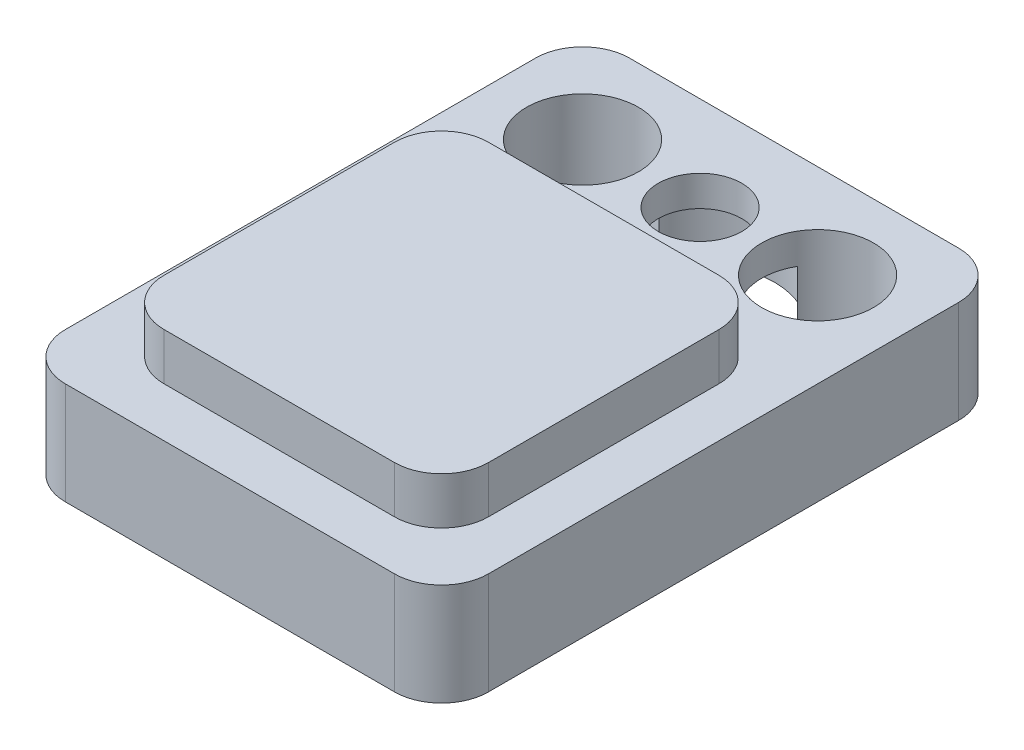
SolidWorks part; units mm, degrees
ref_plane "Front Plane" through (0, 0, 0) normal (0, 0, 1) x (1, 0, 0)
ref_plane "Top Plane" through (0, 0, 0) normal (0, 1, 0) x (1, 0, 0)
ref_plane "Right Plane" through (0, 0, 0) normal (1, 0, 0) x (0, 0, -1)
sketch "Sketch1" plane through (0, 0, 0) normal (0, 1, 0) x (1, 0, 0)
  line L1 (4.5, -6) -> (-4.5, -6)
  line L2 (4.5, -6) -> (4.5, 6)
  line L3 (4.5, 6) -> (-4.5, 6)
  line L4 (-4.5, -6) -> (-4.5, 6)
  line L5 (4.5, -6) -> (-4.5, 6) construction
  line L6 (4.5, 6) -> (-4.5, -6) construction
  point P0 (0, 0)
  dimension "D1" = 9
  dimension "D2" = 12
extrude "Extrude1" add sketch "Sketch1" along normal blind 2.175
sketch "Sketch3" plane through (0, 2.175, 0) normal (0, 1, 0) x (1, 0, 0)
  line L0 (-4.5, 6) -> (-4.5, -6) construction
  line L1 (-3.45, -4.95) -> (3.45, -4.95)
  line L2 (-3.45, -4.95) -> (-3.45, 1.95)
  line L3 (-3.45, 1.95) -> (3.45, 1.95)
  line L4 (3.45, -4.95) -> (3.45, 1.95)
  line L5 (-4.5, -6) -> (4.5, -6) construction
  dimension "D1" = 6.9
  dimension "D2" = 6.9
  dimension "D3" = 1.05
  dimension "D4" = 1.05
extrude "Extrude3" add sketch "Sketch3" along normal blind 1
hole_wizard "CBORE for #0 Socket Head Cap Screw1" positions "3DSketch3" profile "Sketch8" counterbore size "#0" standard "Ansi Inch" end condition through all
sketch3d "3DSketch3"
  line L0 (4.5, 0, -6) -> (-4.5, 0, -6) construction
  line L1 (-4.5, 0, -6) -> (-4.5, 0, 6) construction
  point P0 (0, 0, -4)
  dimension "D1" = 2
  dimension "D2" = 4.5
sketch "Sketch8" plane through (0, 0, -4) normal (1, 0, 0) x (0, 0, -1)
  line L0 (0, 0) -> (0, 3.175)
  line L1 (0, 3.175) -> (0.889, 3.175)
  line L3 (0.889, 3.175) -> (0.889, 1.524)
  line L4 (0.889, 1.524) -> (1.5875, 1.524)
  line L5 (1.5875, 1.524) -> (1.5875, 0)
  line L7 (1.5875, 0) -> (0, 0)
  line L11 (0, -6.35) -> (0, 107.95) construction
  dimension "Thru Hole Dia." = 1.778
  dimension "Thru Hole Depth" = 3.175
  dimension "C'Bore Dia." = 3.175
  dimension "C'Bore Depth" = 1.524
hole_wizard "3/32 (0.09375) Diameter Hole1" positions "3DSketch4" profile "Sketch9" hole size "3/32" standard "Ansi Inch"
sketch3d "3DSketch4"
  line L0 (4.5, 0, -6) -> (-4.5, 0, -6) construction
  line L1 (-4.5, 0, -6) -> (-4.5, 0, 6) construction
  line L2 (4.5, 0, 6) -> (4.5, 0, -6) construction
  point P0 (-2.5, 0, -4)
  point P2 (2.5, 0, -4)
  dimension "D1" = 2
  dimension "D2" = 2
  dimension "D3" = 2
  dimension "D4" = 2
sketch "Sketch9" plane through (-2.5, 0, -4) normal (1, 0, 0) x (0, 0, -1)
  line L0 (0, 0) -> (0, 10.7154)
  line L1 (0, 10.7154) -> (1.1906, 10)
  line L2 (1.1906, 10) -> (1.1906, 0)
  line L5 (1.1906, 0) -> (0, 0)
  line L10 (0, 10.7154) -> (-1.1906, 10) construction
  line L11 (0, -6.35) -> (0, 107.95) construction
  dimension "Hole Dia." = 2.3812
  dimension "Hole Depth" = 10
  dimension "Drill Angle" = 118
fillet "Fillet1" radius 1 8 edges at (-4.5, 1.0875, 6) (-3.45, 2.675, 4.95) (-3.45, 2.675, -1.95) (-4.5, 1.0875, -6) (4.5, 1.0875, 6) (3.45, 2.675, 4.95) (3.45, 2.675, -1.95) (4.5, 1.0875, -6)
